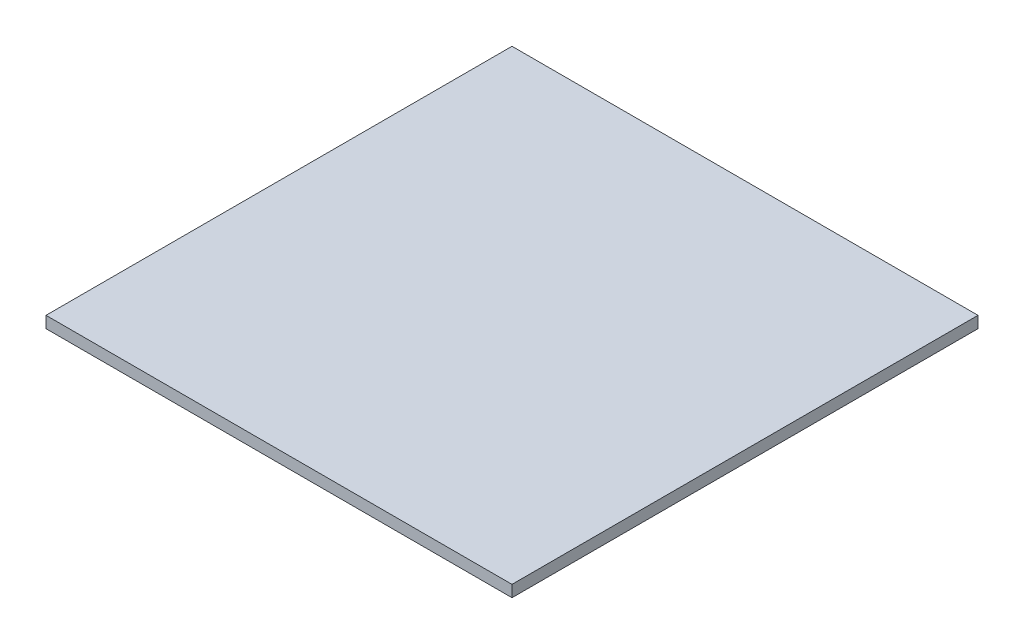
SolidWorks part; units mm, degrees
material "Black Acrylic"
ref_plane "Front Plane" through (0, 0, 0) normal (0, 0, 1) x (1, 0, 0)
ref_plane "Top Plane" through (0, 0, 0) normal (0, 1, 0) x (1, 0, 0)
ref_plane "Right Plane" through (0, 0, 0) normal (1, 0, 0) x (0, 0, -1)
sketch "Sketch1" plane through (0, 0, 0) normal (0, 1, 0) x (1, 0, 0)
  line L1 (-90.5, -90.5) -> (90.5, -90.5)
  line L2 (-90.5, -90.5) -> (-90.5, 90.5)
  line L3 (-90.5, 90.5) -> (90.5, 90.5)
  line L4 (90.5, -90.5) -> (90.5, 90.5)
  line L5 (-90.5, -90.5) -> (90.5, 90.5) construction
  line L6 (-90.5, 90.5) -> (90.5, -90.5) construction
  point P0 (0, 0)
  dimension "D1" = 181
  dimension "D2" = 181
extrude "Boss-Extrude1" add sketch "Sketch1" along normal mid plane 4.5
